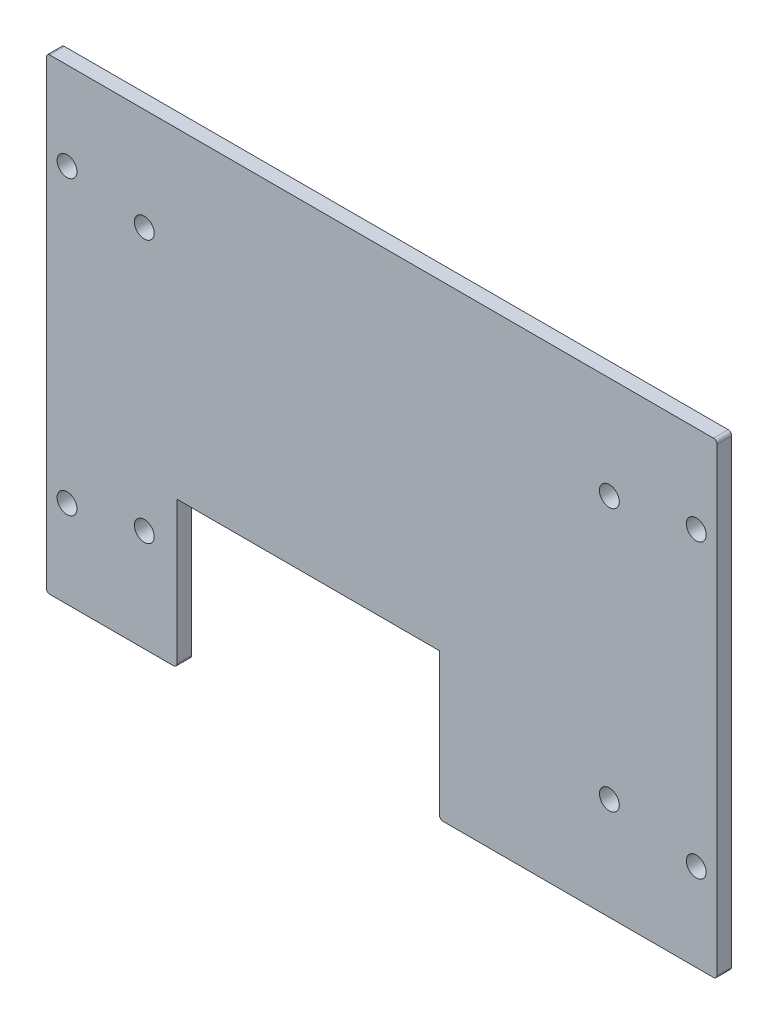
SolidWorks part; units mm, degrees
ref_plane "Front Plane" through (0, 0, 0) normal (0, 0, 1) x (1, 0, 0)
ref_plane "Top Plane" through (0, 0, 0) normal (0, 1, 0) x (1, 0, 0)
ref_plane "Right Plane" through (0, 0, 0) normal (1, 0, 0) x (0, 0, -1)
sketch "Sketch1" plane through (0, 0, 0) normal (0, 0, 1) x (1, 0, 0)
  line L1 (0, 101.6) -> (145.8854, 101.6)
  line L2 (0, 101.6) -> (0, 0)
  line L3 (0, 0) -> (145.8854, 0)
  line L4 (145.8854, 101.6) -> (145.8854, 0)
  dimension "D1" = 101.6
  dimension "D2" = 145.8854
extrude "Boss-Extrude1" add sketch "Sketch1" along normal blind 3.2004
sketch "Sketch4" plane through (0, 0, 3.2004) normal (0, 0, 1) x (1, 0, 0)
  line L0 (0, 101.6) -> (0, 0) construction
  line L1 (28.4328, 31.75) -> (85.5328, 31.75)
  line L2 (28.4328, 31.75) -> (28.4328, 0)
  line L3 (28.4328, 0) -> (85.5328, 0)
  line L4 (85.5328, 31.75) -> (85.5328, 0)
  line L5 (0, 0) -> (145.8854, 0) construction
  dimension "D1" = 28.4328
  dimension "D2" = 57.1
  dimension "D3" = 31.75
extrude "Cut-Extrude1" cut sketch "Sketch4" against normal up to surface (3.2004 mm away) up to face at (72.9427, 50.8, 0)
sketch "Sketch5" plane through (0, 0, 3.2004) normal (0, 0, 1) x (1, 0, 0)
  line L0 (0, 50.8) -> (4.5085, 50.8) construction
  line L1 (4.5085, 19.05) -> (4.5085, 82.55) construction
  line L2 (141.3769, 50.8) -> (145.8854, 50.8) construction
  line L3 (141.3769, 19.05) -> (141.3769, 82.55) construction
  line L4 (0, 101.6) -> (0, 0) construction
  line L5 (145.8854, 0) -> (145.8854, 101.6) construction
  line L6 (21.3199, 50.8) -> (4.5085, 50.8) construction
  line L7 (141.3769, 50.8) -> (122.4729, 50.8) construction
  line L8 (21.3199, 79.375) -> (21.3199, 22.225) construction
  line L9 (122.4729, 79.375) -> (122.4729, 22.225) construction
  line L10 (72.9427, 101.6) -> (72.9427, 0) construction
  line L11 (145.8854, 101.6) -> (0, 101.6) construction
  line L12 (85.5328, 0) -> (145.8854, 0) construction
  circle A0 centre (141.3769, 82.55) radius 2.159
  circle A1 centre (141.3769, 19.05) radius 2.159
  circle A2 centre (4.5085, 19.05) radius 2.159
  circle A3 centre (4.5085, 82.55) radius 2.159
  circle A4 centre (21.3199, 79.375) radius 2.159
  circle A5 centre (21.3199, 22.225) radius 2.159
  circle A6 centre (122.4729, 79.375) radius 2.159
  circle A7 centre (122.4729, 22.225) radius 2.159
  dimension "D3" = 4.318
  dimension "D1" = 4.5085
  dimension "D6" = 4.318
  dimension "D2" = 63.5
  dimension "D4" = 57.15
  dimension "D5" = 21.3199
  dimension "D7" = 23.4124
extrude "Cut-Extrude2" cut sketch "Sketch5" against normal up to surface (3.2004 mm away) up to face at (64.9627, 33.3375, 0)
fillet "Fillet1" radius 0.762 6 edges at (145.8854, 0, 1.6002) (85.5328, 0, 1.6002) (28.4328, 0, 1.6002) (0, 0, 1.6002) (145.8854, 101.6, 1.6002) (0, 101.6, 1.6002)
